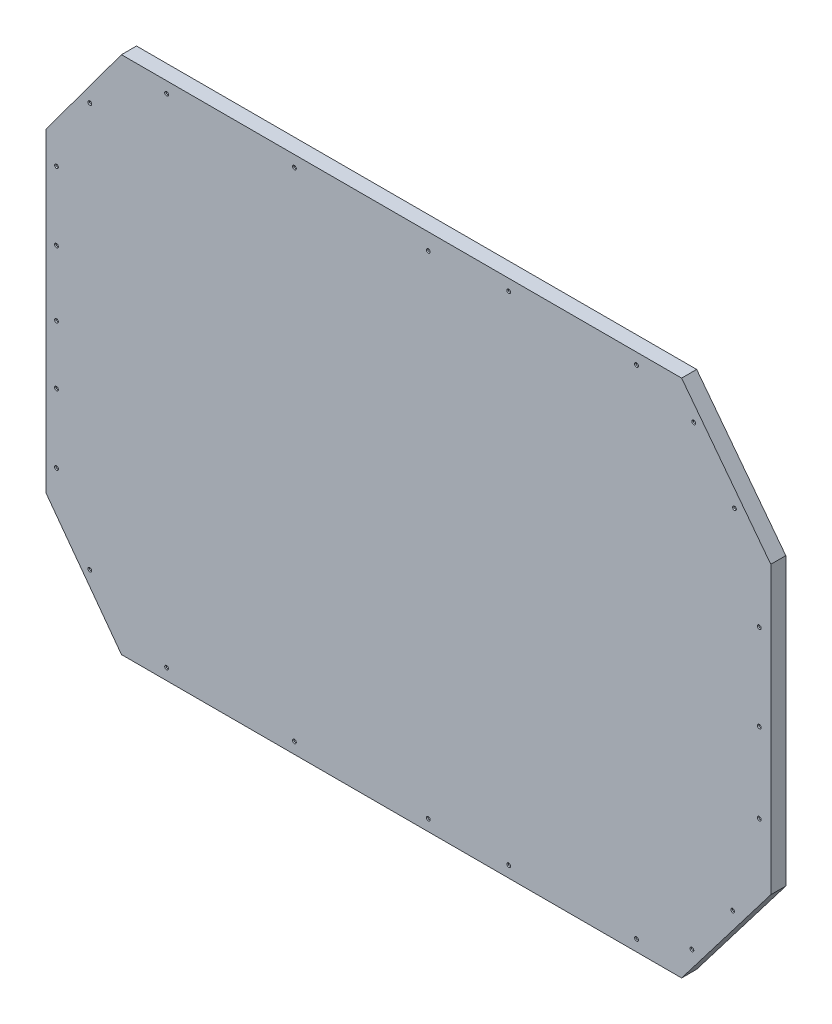
SolidWorks part; units mm, degrees
ref_plane "Front Plane" through (0, 0, 0) normal (0, 0, 1) x (1, 0, 0)
ref_plane "Top Plane" through (0, 0, 0) normal (0, 1, 0) x (1, 0, 0)
ref_plane "Right Plane" through (0, 0, 0) normal (1, 0, 0) x (0, 0, -1)
sketch "Sketch1" plane through (0, 0, 0) normal (0, 0, 1) x (1, 0, 0)
  line L77 (-439.5279, -315.4877) -> (-439.5279, -340.4877)
  line L78 (-469.5279, -315.4877) -> (-439.5279, -315.4877)
  line L79 (-469.5279, -340.4877) -> (-469.5279, -315.4877)
  line L80 (-32.5279, -20) -> (-32.5279, 10)
  line L81 (-32.5279, 10) -> (-5.3287, 10)
  line L82 (-5.3287, -20) -> (-32.5279, -20)
  line L83 (-926.2379, 10) -> (-926.2379, -20)
  line L84 (-926.2379, -20) -> (-956.2379, -20)
  line L85 (-956.2379, 10) -> (-926.2379, 10)
  line L87 (-469.5279, 305.4877) -> (-469.5279, 335.4877)
  line L88 (-439.5279, 305.4877) -> (-469.5279, 305.4877)
  line L89 (-439.5279, 335.4877) -> (-439.5279, 305.4877)
  line L90 (-818.58, 340.4877) -> (-863.58, 340.4877)
  line L91 (-813.58, 335.4877) -> (-813.58, 330.4877)
  line L92 (-793.58, 330.4877) -> (-793.58, 335.4877)
  line L93 (-643.58, 335.4877) -> (-643.58, 330.4877)
  line L94 (-623.58, 330.4877) -> (-623.58, 335.4877)
  line L95 (-648.58, 340.4877) -> (-788.58, 340.4877)
  line L96 (-338.58, 330.4877) -> (-338.58, 335.4877)
  line L97 (-358.58, 335.4877) -> (-358.58, 330.4877)
  line L98 (-363.58, 340.4877) -> (-618.58, 340.4877)
  line L99 (-193.58, 340.4877) -> (-333.58, 340.4877)
  line L100 (-188.58, 335.4877) -> (-188.58, 330.4877)
  line L101 (-168.58, 330.4877) -> (-168.58, 335.4877)
  line L102 (-118.58, 340.4877) -> (-163.58, 340.4877)
  line L103 (-118.58, 340.4877) -> (-106.5388, 324.5187)
  line L104 (-82.4563, 292.5808) -> (-52.3531, 252.6583)
  line L105 (-28.2706, 220.7204) -> (-5.3287, 190.295)
  line L106 (-5.3287, 190.295) -> (-5.3287, 130.295)
  line L107 (-5.3287, 90.295) -> (-5.3287, -90.295)
  line L108 (-5.3287, -130.295) -> (-5.3287, -190.295)
  line L109 (-5.3287, -190.295) -> (-30.6742, -223.908)
  line L110 (-54.7567, -255.8459) -> (-84.8598, -295.7684)
  line L111 (-108.9423, -327.7063) -> (-118.58, -340.4877)
  line L112 (-163.58, -340.4877) -> (-118.58, -340.4877)
  line L113 (-168.58, -330.4877) -> (-168.58, -335.4877)
  line L114 (-188.58, -335.4877) -> (-188.58, -330.4877)
  line L115 (-333.58, -340.4877) -> (-193.58, -340.4877)
  line L116 (-618.58, -340.4877) -> (-363.58, -340.4877)
  line L117 (-358.58, -335.4877) -> (-358.58, -330.4877)
  line L118 (-338.58, -330.4877) -> (-338.58, -335.4877)
  line L119 (-813.58, -335.4877) -> (-813.58, -330.4877)
  line L120 (-623.58, -330.4877) -> (-623.58, -335.4877)
  line L121 (-643.58, -335.4877) -> (-643.58, -330.4877)
  line L122 (-793.58, -330.4877) -> (-793.58, -335.4877)
  line L123 (-910.6084, -259.9442) -> (-918.6489, -265.8789)
  line L124 (-906.7717, -281.9704) -> (-898.7313, -276.0357)
  line L125 (-960.0195, -209.8289) -> (-918.6489, -265.8789)
  line L126 (-950.0195, -163.7655) -> (-960.0195, -163.7655)
  line L127 (-960.0195, -183.7655) -> (-950.0195, -183.7655)
  line L128 (-950.0195, -72.3515) -> (-960.0195, -72.3515)
  line L129 (-960.0195, -92.3515) -> (-950.0195, -92.3515)
  line L130 (-960.0195, 92.3405) -> (-950.0195, 92.3405)
  line L131 (-950.0195, 72.3405) -> (-960.0195, 72.3405)
  line L132 (-960.0195, 183.7545) -> (-950.0195, 183.7545)
  line L133 (-950.0195, 163.7545) -> (-960.0195, 163.7545)
  line L134 (-918.6541, 265.8719) -> (-960.0195, 209.8289)
  line L135 (-910.6084, 259.9333) -> (-918.6541, 265.8719)
  line L136 (-906.777, 281.9633) -> (-898.7313, 276.0247)
  line L137 (-863.58, 340.4877) -> (-906.777, 281.9633)
  line L138 (-963.71, 209.8289) -> (-863.58, 345.4877)
  line L139 (-960.0195, 209.8289) -> (-960.0195, 183.7545)
  line L140 (-960.0195, 163.7545) -> (-960.0195, 92.3405)
  line L141 (-960.0195, 72.3405) -> (-960.0195, -72.3515)
  line L142 (-960.0195, -92.3515) -> (-960.0195, -163.7655)
  line L143 (-963.71, -209.8289) -> (-963.71, 209.8289)
  line L144 (-960.0195, -183.7655) -> (-960.0195, -209.8289)
  line L145 (-906.7717, -281.9704) -> (-863.58, -340.4877)
  line L146 (-863.58, -340.4877) -> (-818.58, -340.4877)
  line L147 (-863.58, -345.4877) -> (-963.71, -209.8289)
  line L148 (-118.58, 345.4877) -> (-863.58, 345.4877)
  line L149 (0, 190.295) -> (-118.58, 345.4877)
  line L150 (0, -190.295) -> (0, 190.295)
  line L151 (-118.58, -345.4877) -> (0, -190.295)
  line L152 (-788.58, -340.4877) -> (-648.58, -340.4877)
  line L153 (-863.58, -345.4877) -> (-118.58, -345.4877)
  circle A68 centre (-803.58, 330.4877) radius 1.5
  arc A69 (-813.58, 335.4877) -> (-818.58, 340.4877) centre (-818.58, 335.4877) ccw
  arc A70 (-813.58, 330.4877) -> (-793.58, 330.4877) centre (-803.58, 330.4877) ccw
  arc A71 (-788.58, 340.4877) -> (-793.58, 335.4877) centre (-788.58, 335.4877) ccw
  circle A72 centre (-633.58, 330.4877) radius 1.5
  arc A73 (-643.58, 330.4877) -> (-623.58, 330.4877) centre (-633.58, 330.4877) ccw
  arc A74 (-618.58, 340.4877) -> (-623.58, 335.4877) centre (-618.58, 335.4877) ccw
  arc A75 (-643.58, 335.4877) -> (-648.58, 340.4877) centre (-648.58, 335.4877) ccw
  arc A76 (-333.58, 340.4877) -> (-338.58, 335.4877) centre (-333.58, 335.4877) ccw
  circle A77 centre (-348.58, 330.4877) radius 1.5
  arc A78 (-358.58, 330.4877) -> (-338.58, 330.4877) centre (-348.58, 330.4877) ccw
  arc A79 (-358.58, 335.4877) -> (-363.58, 340.4877) centre (-363.58, 335.4877) ccw
  arc A80 (-188.58, 335.4877) -> (-193.58, 340.4877) centre (-193.58, 335.4877) ccw
  circle A81 centre (-178.58, 330.4877) radius 1.5
  arc A82 (-188.58, 330.4877) -> (-168.58, 330.4877) centre (-178.58, 330.4877) ccw
  arc A83 (-163.58, 340.4877) -> (-168.58, 335.4877) centre (-163.58, 335.4877) ccw
  arc A84 (-108.5026, 310.5136) -> (-106.5388, 324.5187) centre (-114.5232, 318.4981) ccw
  circle A85 centre (-102.482, 302.5291) radius 1.5
  arc A86 (-108.5026, 310.5136) -> (-96.4614, 294.5446) centre (-102.482, 302.5291) ccw
  arc A87 (-82.4563, 292.5808) -> (-96.4614, 294.5446) centre (-90.4407, 286.5602) ccw
  arc A88 (-54.317, 238.6532) -> (-52.3531, 252.6583) centre (-60.3376, 246.6377) ccw
  circle A89 centre (-48.2964, 230.6687) radius 1.5
  arc A90 (-54.317, 238.6532) -> (-42.2758, 222.6842) centre (-48.2964, 230.6687) ccw
  arc A91 (-28.2706, 220.7204) -> (-42.2758, 222.6842) centre (-36.2551, 214.6997) ccw
  arc A92 (-15.3287, 120.295) -> (-5.3287, 130.295) centre (-15.3287, 130.295) ccw
  circle A93 centre (-15.3287, 110.295) radius 1.5
  arc A94 (-15.3287, 120.295) -> (-15.3287, 100.295) centre (-15.3287, 110.295) ccw
  arc A95 (-5.3287, 90.295) -> (-15.3287, 100.295) centre (-15.3287, 90.295) ccw
  circle A96 centre (-15.3287, -110.295) radius 1.5
  arc A97 (-15.3287, -100.295) -> (-5.3287, -90.295) centre (-15.3287, -90.295) ccw
  arc A98 (-15.3287, -100.295) -> (-15.3287, -120.295) centre (-15.3287, -110.295) ccw
  arc A99 (-5.3287, -130.295) -> (-15.3287, -120.295) centre (-15.3287, -130.295) ccw
  arc A100 (-44.6793, -225.8718) -> (-30.6742, -223.908) centre (-38.6587, -217.8873) ccw
  circle A101 centre (-50.7, -233.8563) radius 1.5
  arc A102 (-54.7567, -255.8459) -> (-56.7206, -241.8408) centre (-62.7412, -249.8253) ccw
  arc A103 (-44.6793, -225.8718) -> (-56.7206, -241.8408) centre (-50.7, -233.8563) ccw
  arc A104 (-98.865, -297.7322) -> (-84.8598, -295.7684) centre (-92.8443, -289.7478) ccw
  circle A105 centre (-104.8856, -305.7167) radius 1.5
  arc A106 (-98.865, -297.7322) -> (-110.9062, -313.7012) centre (-104.8856, -305.7167) ccw
  arc A107 (-108.9423, -327.7063) -> (-110.9062, -313.7012) centre (-116.9268, -321.6857) ccw
  arc A108 (-168.58, -335.4877) -> (-163.58, -340.4877) centre (-163.58, -335.4877) ccw
  circle A109 centre (-178.58, -330.4877) radius 1.5
  arc A110 (-168.58, -330.4877) -> (-188.58, -330.4877) centre (-178.58, -330.4877) ccw
  arc A111 (-193.58, -340.4877) -> (-188.58, -335.4877) centre (-193.58, -335.4877) ccw
  arc A112 (-363.58, -340.4877) -> (-358.58, -335.4877) centre (-363.58, -335.4877) ccw
  arc A113 (-338.58, -335.4877) -> (-333.58, -340.4877) centre (-333.58, -335.4877) ccw
  arc A114 (-338.58, -330.4877) -> (-358.58, -330.4877) centre (-348.58, -330.4877) ccw
  circle A115 centre (-348.58, -330.4877) radius 1.5
  circle A116 centre (-803.58, -330.4877) radius 1.5
  arc A117 (-623.58, -335.4877) -> (-618.58, -340.4877) centre (-618.58, -335.4877) ccw
  arc A118 (-648.58, -340.4877) -> (-643.58, -335.4877) centre (-648.58, -335.4877) ccw
  circle A119 centre (-633.58, -330.4877) radius 1.5
  arc A120 (-623.58, -330.4877) -> (-643.58, -330.4877) centre (-633.58, -330.4877) ccw
  arc A121 (-793.58, -335.4877) -> (-788.58, -340.4877) centre (-788.58, -335.4877) ccw
  arc A122 (-793.58, -330.4877) -> (-813.58, -330.4877) centre (-803.58, -330.4877) ccw
  arc A123 (-818.58, -340.4877) -> (-813.58, -335.4877) centre (-818.58, -335.4877) ccw
  circle A124 centre (-905.6543, -268.7166) radius 1.5
  arc A125 (-898.7313, -276.0357) -> (-910.6084, -259.9442) centre (-904.6698, -267.99) ccw
  circle A126 centre (-950.0195, -173.7655) radius 1.5
  arc A127 (-950.0195, -183.7655) -> (-950.0195, -163.7655) centre (-950.0195, -173.7655) ccw
  circle A128 centre (-950.0195, -82.3515) radius 1.5
  arc A129 (-950.0195, -92.3515) -> (-950.0195, -72.3515) centre (-950.0195, -82.3515) ccw
  arc A130 (-950.0195, 72.3405) -> (-950.0195, 92.3405) centre (-950.0195, 82.3405) ccw
  arc A131 (-950.0195, 163.7545) -> (-950.0195, 183.7545) centre (-950.0195, 173.7545) ccw
  arc A132 (-910.6084, 259.9333) -> (-898.7313, 276.0247) centre (-904.6698, 267.979) ccw
  circle A133 centre (-950.0195, 82.3405) radius 1.5
  circle A134 centre (-950.0195, 173.7545) radius 1.5
  circle A135 centre (-905.6543, 268.7057) radius 1.5
sketch "Sketch2" plane through (0, 0, 0) normal (0, 0, 1) x (1, 0, 0)
  line L0 (-118.58, 345.4877) -> (-863.58, 345.4877) construction
  line L1 (0, 190.295) -> (-118.58, 345.4877) construction
  line L2 (0, -190.295) -> (0, 190.295) construction
  line L3 (-118.58, -345.4877) -> (0, -190.295) construction
  line L4 (-863.58, -345.4877) -> (-118.58, -345.4877) construction
  line L5 (-863.58, -345.4877) -> (-963.71, -209.8289) construction
  line L6 (-963.71, 209.8289) -> (-863.58, 345.4877) construction
  line L7 (-963.71, -209.8289) -> (-963.71, 209.8289) construction
  line L8 (-118.58, 345.4877) -> (-863.58, 345.4877)
  line L9 (0, 190.295) -> (-118.58, 345.4877)
  line L10 (0, -190.295) -> (0, 190.295)
  line L11 (-118.58, -345.4877) -> (0, -190.295)
  line L12 (-863.58, -345.4877) -> (-118.58, -345.4877)
  line L13 (-863.58, -345.4877) -> (-963.71, -209.8289)
  line L14 (-963.71, 209.8289) -> (-863.58, 345.4877)
  line L15 (-963.71, -209.8289) -> (-963.71, 209.8289)
extrude "Boss-Extrude1" add sketch "Sketch2" along normal blind 20
hole_wizard "CSK for #3 Flat Head Machine Screw (100)1" positions "Sketch4" profile "Sketch5" countersink size "#3" standard "ANSI Inch" end condition up to next
sketch "Sketch4" plane through (0, 0, 20) normal (0, 0, 1) x (1, 0, 0)
  point P0 (-950.0195, 82.3405)
  point P3 (-950.0195, 173.7545)
  point P6 (-905.6543, 268.7057)
  point P9 (-803.58, 330.4877)
  point P12 (-633.58, 330.4877)
  point P15 (-455.4802, 323.5214)
  point P17 (-348.58, 330.4877)
  point P20 (-178.58, 330.4877)
  point P23 (-102.482, 302.5291)
  point P26 (-48.2964, 230.6687)
  point P29 (-15.3287, 110.295)
  point P32 (-15.3287, -4.2368)
  point P34 (-15.3287, -110.295)
  point P37 (-50.7, -233.8563)
  point P40 (-104.8856, -305.7167)
  point P43 (-178.58, -330.4877)
  point P46 (-348.58, -330.4877)
  point P49 (-455.4802, -330.4877)
  point P51 (-633.58, -330.4877)
  point P54 (-803.58, -330.4877)
  point P57 (-905.6543, -268.7166)
  point P60 (-950.0195, -173.7655)
  point P63 (-950.0195, -82.3515)
  point P66 (-950.0195, -4.2368)
sketch "Sketch5" plane through (-950.0195, 82.3405, 20) normal (1, 0, 0) x (0, -1, 0)
  line L0 (0, 0) -> (0, 20)
  line L1 (0, 20) -> (1.397, 20)
  line L2 (1.397, 20) -> (1.397, 0.9484)
  line L3 (1.397, 0.9484) -> (2.5273, 0)
  line L5 (2.5273, 0) -> (0, 0)
  line L6 (-1.397, 0.9484) -> (-2.5273, 0) construction
  line L11 (0, -6.35) -> (0, 107.95) construction
  dimension "Thru Hole Dia." = 2.794
  dimension "Thru Hole Depth" = 20
  dimension "Near C'Sink Dia." = 5.0546
  dimension "Near C'Sink Angle" = 100
